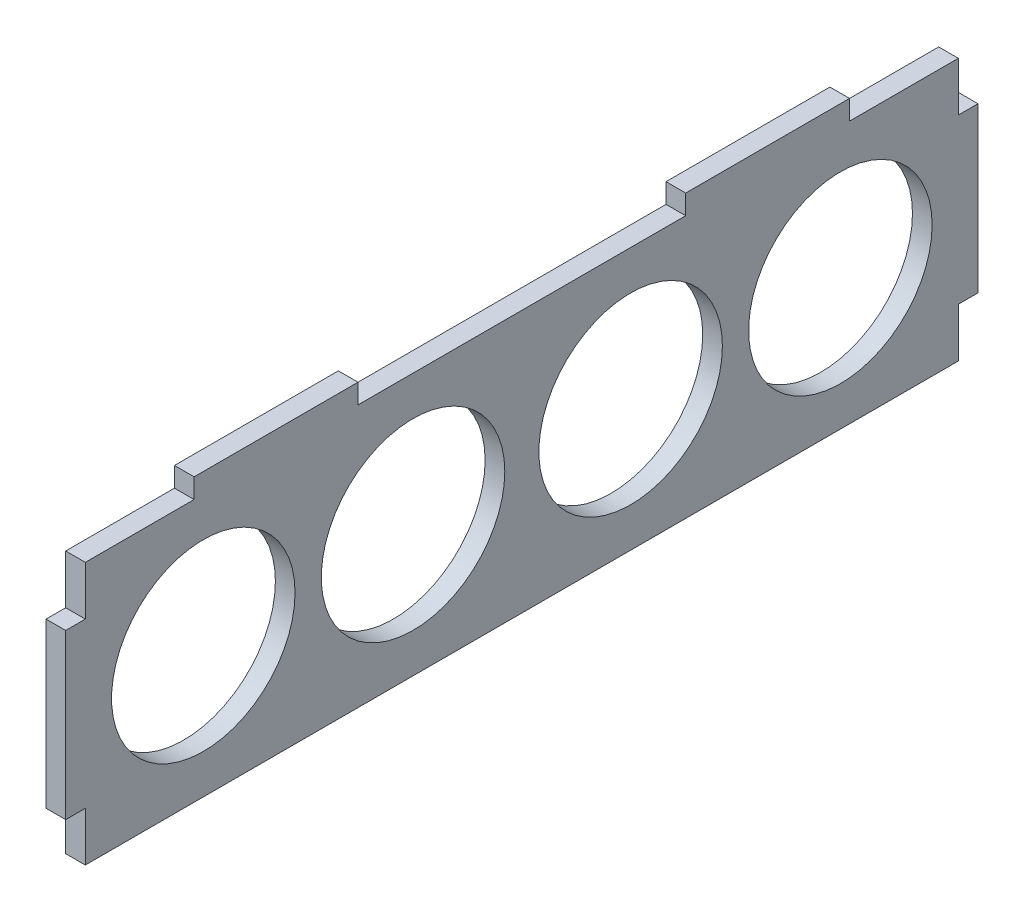
SolidWorks part; units mm, degrees
ref_plane "Front Plane" through (0, 0, 0) normal (0, 0, 1) x (1, 0, 0)
ref_plane "Top Plane" through (0, 0, 0) normal (0, 1, 0) x (1, 0, 0)
ref_plane "Right Plane" through (0, 0, 0) normal (1, 0, 0) x (0, 0, -1)
sketch "Sketch1" plane through (0, 0, 0) normal (1, 0, 0) x (0, 0, -1)
  line L0 (-69.6, 0) -> (69.6, 0) construction
  line L1 (-66.6, -20) -> (66.6, -20)
  line L2 (-66.6, -20) -> (-66.6, 20)
  line L3 (-66.6, 20) -> (66.6, 20)
  line L4 (66.6, -20) -> (66.6, 20)
  line L5 (-66.6, -20) -> (66.6, 20) construction
  line L6 (-66.6, 20) -> (66.6, -20) construction
  line L7 (-66.6, 12.5) -> (-69.6, 12.5)
  line L8 (-66.6, 12.5) -> (-66.6, -12.5)
  line L9 (-66.6, -12.5) -> (-69.6, -12.5)
  line L10 (-69.6, 12.5) -> (-69.6, -12.5)
  line L11 (66.6, 12.5) -> (69.6, 12.5)
  line L12 (66.6, 12.5) -> (66.6, -12.5)
  line L13 (66.6, -12.5) -> (69.6, -12.5)
  line L14 (69.6, 12.5) -> (69.6, -12.5)
  line L15 (-50, 20) -> (-25, 20)
  line L16 (-50, 20) -> (-50, 23)
  line L17 (-50, 23) -> (-25, 23)
  line L18 (-25, 20) -> (-25, 23)
  line L19 (25, 20) -> (50, 20)
  line L20 (25, 20) -> (25, 23)
  line L21 (25, 23) -> (50, 23)
  line L22 (50, 20) -> (50, 23)
  circle A0 centre (-48.6, 0) radius 14
  circle A4 centre (48.6, 0) radius 14
  circle A5 centre (-16.6, 0) radius 14
  circle A6 centre (16.6, 0) radius 14
  point P0 (0, 0)
  point P22 (-69.6, 0)
  point P23 (69.6, 0)
  dimension "D5" = 28
  dimension "D8" = 18
  dimension "D9" = 50
  dimension "D1" = 25
  dimension "D2" = 3
  dimension "D3" = 25
  dimension "D4" = 25
  dimension "D6" = 18
  dimension "D7" = 40
  dimension "D10" = 133.2
  dimension "D11" = 50
extrude "Boss-Extrude1" add sketch "Sketch1" along normal blind 3
